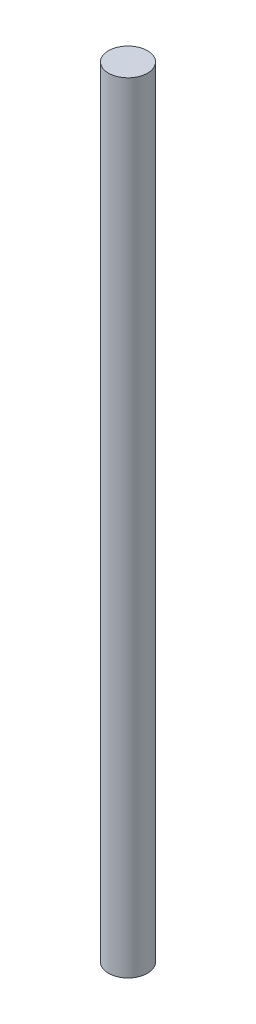
SolidWorks part; units mm, degrees
ref_plane "前视基准面" through (0, 0, 0) normal (0, 0, 1) x (1, 0, 0)
ref_plane "上视基准面" through (0, 0, 0) normal (0, 1, 0) x (1, 0, 0)
ref_plane "右视基准面" through (0, 0, 0) normal (1, 0, 0) x (0, 0, -1)
sketch "草图1" plane through (0, 0, 0) normal (0, 1, 0) x (1, 0, 0)
  circle A0 centre (0, 0) radius 7.5
  dimension "D1" = 15
extrude "凸台-拉伸1" add sketch "草图1" along normal blind 300
